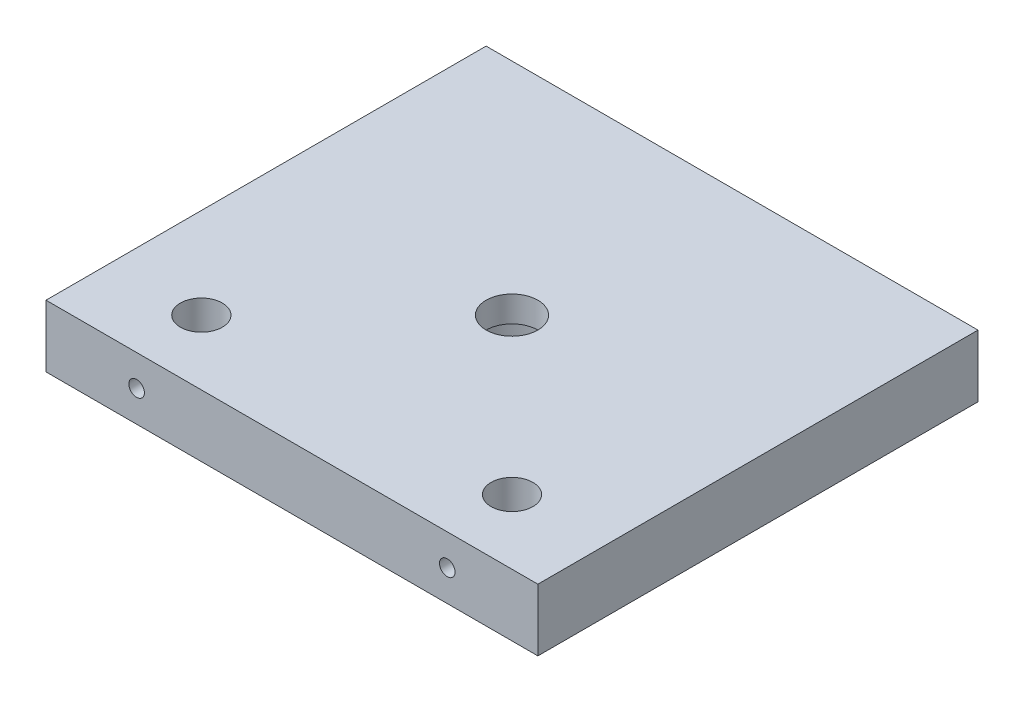
SolidWorks part; units mm, degrees
ref_plane "Front Plane" through (0, 0, 0) normal (0, 0, 1) x (1, 0, 0)
ref_plane "Top Plane" through (0, 0, 0) normal (0, 1, 0) x (1, 0, 0)
ref_plane "Right Plane" through (0, 0, 0) normal (1, 0, 0) x (0, 0, -1)
sketch "Sketch1" plane through (0, 0, 0) normal (0, 0, 1) x (1, 0, 0)
  line L1 (-47.5, 6) -> (47.5, 6)
  line L2 (-47.5, 6) -> (-47.5, -6)
  line L3 (-47.5, -6) -> (47.5, -6)
  line L4 (47.5, 6) -> (47.5, -6)
  line L5 (-47.5, 6) -> (47.5, -6) construction
  line L6 (-47.5, -6) -> (47.5, 6) construction
  point P0 (0, 0)
  dimension "D1" = 12
  dimension "D2" = 95
extrude "Boss-Extrude1" add sketch "Sketch1" along normal blind 85
sketch "Sketch2" plane through (0, -6, 0) normal (0, -1, 0) x (1, 0, 0)
  line L0 (-47.5, 85) -> (47.5, 85) construction
  line L1 (-47.5, 85) -> (-47.5, 0) construction
  line L2 (47.5, 85) -> (47.5, 0) construction
  line L3 (47.5, 85) -> (-47.5, 85) construction
  circle A0 centre (-30, 72.5) radius 4.05
  circle A1 centre (30, 72.5) radius 4.05
  circle A2 centre (0, 42.5) radius 5
  point P13 (0, 85)
  dimension "D1" = 8.1
  dimension "D2" = 8.1
  dimension "D3" = 10
  dimension "D4" = 12.5
  dimension "D5" = 17.5
  dimension "12.5" = 12.5
  dimension "D6" = 42.5
  dimension "D7" = 17.5
  dimension "D8" = 47.5
extrude "Cut-Extrude1" cut sketch "Sketch2" against normal through all
sketch "Sketch3" plane through (0, -6, 0) normal (0, -1, 0) x (1, 0, 0)
  circle A0 centre (0, 42.5) radius 11.05
  dimension "D1" = 22.1
extrude "Cut-Extrude2" cut sketch "Sketch3" against normal blind 7
sketch "Sketch4" plane through (0, 0, 85) normal (0, 0, 1) x (1, 0, 0)
  line L0 (47.5, -6) -> (47.5, 6) construction
  line L1 (-47.5, 6) -> (-47.5, -6) construction
  circle A0 centre (30, 0) radius 1.5
  circle A1 centre (-30, 0) radius 1.5
  point P4 (47.5, 0)
  point P7 (-47.5, 0)
  dimension "D1" = 3
  dimension "D2" = 3
  dimension "D3" = 17.5
  dimension "D4" = 17.5
extrude "Cut-Extrude3" cut sketch "Sketch4" against normal up to next
